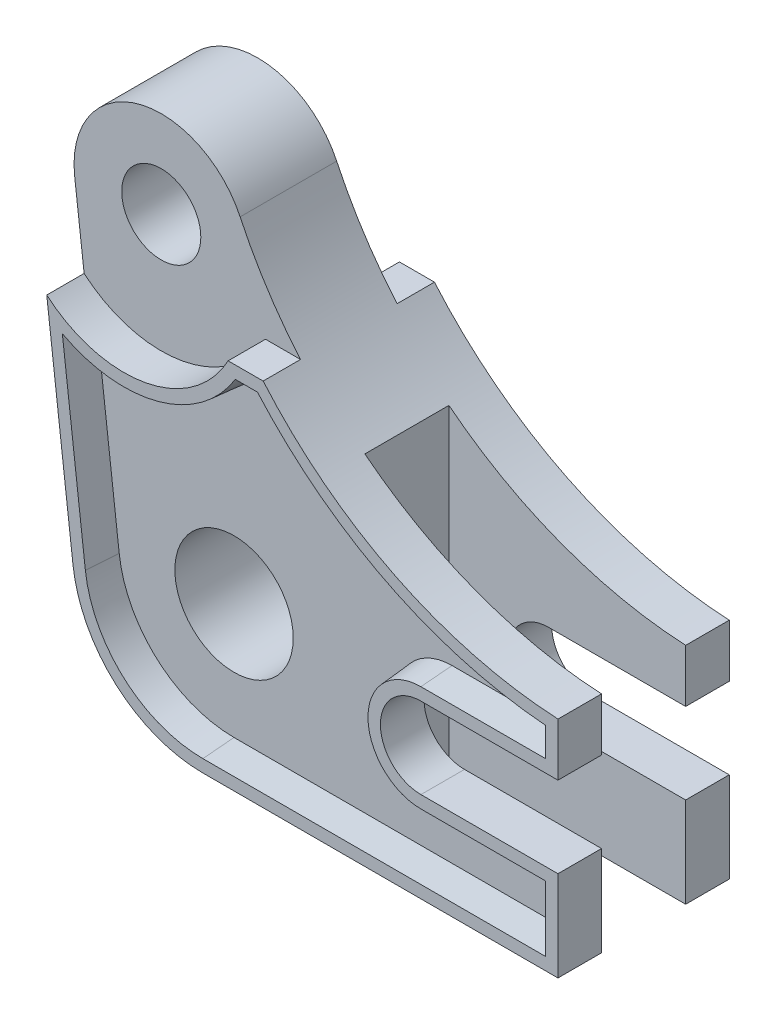
SolidWorks part; units mm, degrees
material "AISI 1020"
ref_plane "Front" through (0, 0, 0) normal (0, 0, 1) x (1, 0, 0)
ref_plane "Top" through (0, 0, 0) normal (0, 1, 0) x (1, 0, 0)
ref_plane "Right" through (0, 0, 0) normal (1, 0, 0) x (0, 0, -1)
sketch "Sketch1" plane through (0, 0, 0) normal (0, 0, 1) x (1, 0, 0)
  line L0 (0, 0) -> (0, 14.5)
  line L1 (0, 14.5) -> (-22, 14.5)
  line L2 (-22, 27.5) -> (0, 27.5)
  line L3 (0, 27.5) -> (0, 36)
  line L4 (-83.584, 66.6759) -> (-77.8528, 18.5183)
  line L5 (-57, 0) -> (0, 0)
  line L6 (-57, 21) -> (-57, 51.297) construction
  line L7 (-69.6821, 68.3304) -> (-57, 21) construction
  arc A0 (-22, 14.5) -> (-22, 27.5) centre (-22, 21) cw
  arc A1 (0, 36) -> (-57.0216, 74.3062) centre (3.5681, 102.9049) cw
  arc A2 (-57.0216, 74.3062) -> (-83.584, 66.6759) centre (-69.6821, 68.3304) ccw
  arc A3 (-77.8528, 18.5183) -> (-57, 0) centre (-57, 21) ccw
  circle A4 centre (-69.6821, 68.3304) radius 6.35
  circle A5 centre (-57, 21) radius 9.5
  dimension "D4" = 13
  dimension "D6" = 21
  dimension "D7" = 67
  dimension "D8" = 14
  dimension "D9" = 19
  dimension "D10" = 12.7
  dimension "D1" = 57
  dimension "D2" = 22
  dimension "D3" = 21
  dimension "D5" = 36
  dimension "D12" = 15
  dimension "D11" = 49
extrude "Boss-Extrude1" add sketch "Sketch1" along normal mid plane 27.5
sketch "Sketch3" plane through (0, 0, 13.75) normal (0, 0, 1) x (1, 0, 0)
  line L0 (-83.584, 66.6759) -> (-77.8528, 18.5183) construction
  line L1 (-83.584, 66.6759) -> (-82.066, 53.9207)
  line L2 (-52.9489, 59.3304) -> (-47.3265, 59.3304)
  arc A0 (-82.066, 53.9207) -> (-52.9489, 59.3304) centre (-69.6821, 68.3304) ccw
  arc A1 (-57.0216, 74.3062) -> (0, 36) centre (3.5681, 102.9049) ccw construction
  arc A2 (-57.0216, 74.3062) -> (0, 36) centre (3.5681, 102.9049) ccw
  arc A3 (-57.0216, 74.3062) -> (-83.584, 66.6759) centre (-69.6821, 68.3304) ccw construction
  arc A4 (-57.0216, 74.3062) -> (-83.584, 66.6759) centre (-69.6821, 68.3304) ccw
  arc M8 (0, 36) -> (-57.0216, 74.3062) centre (3.5681, 102.9049) cw
  arc M9 (-57.0216, 74.3062) -> (-83.584, 66.6759) centre (-69.6821, 68.3304) ccw
  line M10 (-83.584, 66.6759) -> (-77.8528, 18.5183)
  circle M12 centre (-69.6821, 68.3304) radius 6.35
  dimension "D1" = 19
  dimension "D2" = 9
extrude "Cut-Extrude1" cut sketch "Sketch3" against normal blind 6 contours A0 L2 M10 M8 M9 M12
mirror "Mirror1" about plane through (0, 0, 0) normal (0, 0, 1) of "Cut-Extrude1"
sketch "Sketch4" plane through (0, 0, 0) normal (0, -1, 0) x (1, 0, 0)
  line L0 (0, 6.75) -> (-38, 6.75)
  line L1 (0, 13.75) -> (0, -13.75) construction
  line L2 (-38, 6.75) -> (-38, -6.75)
  line L3 (-38, -6.75) -> (0, -6.75)
  line L4 (0, -6.75) -> (0, 6.75)
  line L5 (-57, 13.75) -> (0, 13.75) construction
  line L6 (-57, -13.75) -> (0, -13.75) construction
  dimension "D1" = 7
  dimension "D2" = 7
  dimension "D3" = 38
extrude "Cut-Extrude2" cut sketch "Sketch4" against normal through all
sketch "Sketch5" plane through (0, 0, 13.75) normal (0, 0, 1) x (1, 0, 0)
  line L0 (-52.9489, 59.3304) -> (-47.3265, 59.3304) construction
  line L1 (-82.066, 53.9207) -> (-77.8528, 18.5183) construction
  line L2 (-57, 0) -> (0, 0) construction
  line L3 (0, 27.5) -> (0, 36) construction
  line L4 (-22, 27.5) -> (0, 27.5) construction
  line L5 (0, 14.5) -> (-22, 14.5) construction
  line L6 (0, 0) -> (0, 14.5) construction
  line L21 (-52.9489, 59.3304) -> (-47.3265, 59.3304)
  line L22 (0, 27.5) -> (0, 36)
  line L23 (-22, 27.5) -> (0, 27.5)
  line L24 (0, 14.5) -> (-22, 14.5)
  line L25 (0, 0) -> (0, 14.5)
  line L26 (-57, 0) -> (0, 0)
  line L27 (-82.066, 53.9207) -> (-77.8528, 18.5183)
  line L28 (-51.7936, 57.3304) -> (-48.2388, 57.3304)
  line L29 (-2, 29.5) -> (-2, 34.13)
  line L30 (-22, 29.5) -> (-2, 29.5)
  line L31 (-2, 12.5) -> (-22, 12.5)
  line L32 (-2, 2) -> (-2, 12.5)
  line L33 (-57, 2) -> (-2, 2)
  line L34 (-79.5615, 49.7993) -> (-75.8669, 18.7547)
  arc A0 (-82.066, 53.9207) -> (-52.9489, 59.3304) centre (-69.6821, 68.3304) ccw construction
  arc A1 (-77.8528, 18.5183) -> (-57, 0) centre (-57, 21) ccw construction
  arc A2 (-47.3265, 59.3304) -> (0, 36) centre (3.5681, 102.9049) ccw construction
  arc A3 (-22, 27.5) -> (-22, 14.5) centre (-22, 21) ccw construction
  arc A12 (-47.3265, 59.3304) -> (0, 36) centre (3.5681, 102.9049) ccw
  arc A13 (-22, 27.5) -> (-22, 14.5) centre (-22, 21) ccw
  arc A14 (-77.8528, 18.5183) -> (-57, 0) centre (-57, 21) ccw
  arc A15 (-82.066, 53.9207) -> (-52.9489, 59.3304) centre (-69.6821, 68.3304) ccw
  arc A16 (-48.2388, 57.3304) -> (-2, 34.13) centre (3.5681, 102.9049) ccw
  arc A17 (-22, 29.5) -> (-22, 12.5) centre (-22, 21) ccw
  arc A18 (-75.8669, 18.7547) -> (-57, 2) centre (-57, 21) ccw
  arc A19 (-79.5615, 49.7993) -> (-51.7936, 57.3304) centre (-69.6821, 68.3304) ccw
  circle M12 centre (-57, 21) radius 9.5
  dimension "D1" = 2
extrude "Cut-Extrude3" cut sketch "Sketch5" against normal blind 5 draft 5 contours A19 L34 A18 L33 L32 L31 A17 L30 L29 A16 L28 M12 | M12
equation "\"A\"=57"
equation "\"D1@Sketch1\"=\"A\""
equation "\"B\"=21"
equation "\"D3@Sketch1\"=\"B\""
equation "\"C\"= 27.5"
equation "\"D6@Sketch1\"=\"B\""
equation "\"D1@Boss-Extrude1\"=\"C\""
